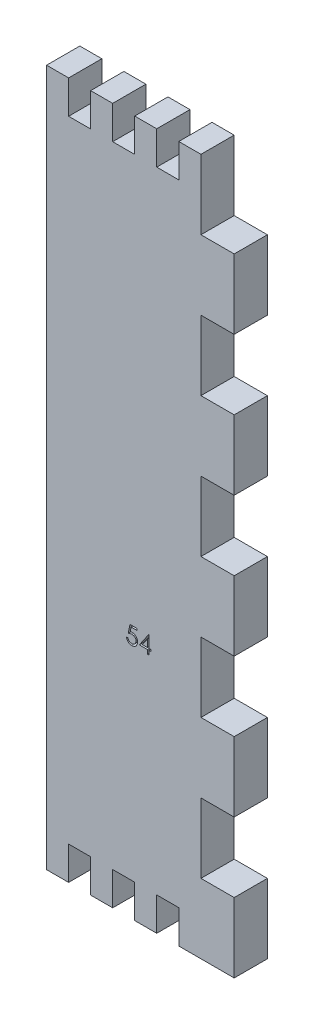
SolidWorks part; units mm, degrees
material "Acrylic (Medium-high impact)"
ref_plane "Front Plane" through (0, 0, 0) normal (0, 0, 1) x (1, 0, 0)
ref_plane "Top Plane" through (0, 0, 0) normal (0, 1, 0) x (1, 0, 0)
ref_plane "Right Plane" through (0, 0, 0) normal (1, 0, 0) x (0, 0, -1)
sketch "Sketch1" plane through (0, 0, 0) normal (0, 0, 1) x (1, 0, 0)
  line L0 (-47.3809, 0) -> (122.7457, 0) construction
  line L1 (0, 130) -> (4.11, 130)
  line L2 (0, 130) -> (0, 0)
  line L3 (0, 0) -> (35, 0)
  line L4 (35, 117) -> (35, 104)
  line L9 (28.8, 52) -> (35, 52)
  line L10 (28.8, 52) -> (28.8, 39)
  line L11 (28.8, 39) -> (35, 39)
  line L17 (28.8, 104) -> (35, 104)
  line L18 (28.8, 104) -> (28.8, 91)
  line L19 (28.8, 91) -> (35, 91)
  line L21 (28.8, 78) -> (35, 78)
  line L22 (28.8, 78) -> (28.8, 65)
  line L23 (28.8, 65) -> (35, 65)
  line L29 (28.8, 26) -> (35, 26)
  line L30 (28.8, 26) -> (28.8, 13)
  line L31 (28.8, 13) -> (35, 13)
  line L34 (28.8, 130) -> (28.8, 117)
  line L35 (28.8, 117) -> (35, 117)
  line L37 (0, 65.7628) -> (0, -41.6741) construction
  line L38 (35, 91) -> (35, 78)
  line L39 (35, 65) -> (35, 52)
  line L40 (35, 39) -> (35, 26)
  line L41 (35, 13) -> (35, 0)
  line L42 (8.22, 130) -> (12.33, 130)
  line L43 (4.11, 0) -> (8.22, 0)
  line L44 (4.11, 0) -> (4.11, 6.2)
  line L45 (4.11, 6.2) -> (8.22, 6.2)
  line L46 (8.22, 0) -> (8.22, 6.2)
  line L47 (12.33, 0) -> (16.44, 0)
  line L48 (12.33, 0) -> (12.33, 6.2)
  line L49 (12.33, 6.2) -> (16.44, 6.2)
  line L50 (16.44, 0) -> (16.44, 6.2)
  line L51 (20.55, 6.2) -> (24.66, 6.2)
  line L52 (20.55, 6.2) -> (20.55, 0)
  line L53 (20.55, 0) -> (24.66, 0)
  line L54 (24.66, 6.2) -> (24.66, 0)
  line L68 (4.11, 130) -> (4.11, 123.8)
  line L69 (4.11, 123.8) -> (8.22, 123.8)
  line L70 (8.22, 130) -> (8.22, 123.8)
  line L72 (12.33, 130) -> (12.33, 123.8)
  line L73 (12.33, 123.8) -> (16.44, 123.8)
  line L74 (16.44, 130) -> (16.44, 123.8)
  line L76 (20.55, 130) -> (20.55, 123.8)
  line L77 (20.55, 123.8) -> (24.66, 123.8)
  line L78 (24.66, 130) -> (24.66, 123.8)
  line L79 (16.44, 130) -> (20.55, 130)
  line L80 (24.66, 130) -> (28.8, 130)
  dimension "D1" = 130
  dimension "D2" = 35
  dimension "D3" = 6.2
  dimension "D4" = 13
  dimension "D5" = 13
  dimension "D6" = 6.2
  dimension "D7" = 13
  dimension "D8" = 6.2
  dimension "D9" = 6.2
  dimension "D10" = 6.2
  dimension "D11" = 13
  dimension "D12" = 13
  dimension "D13" = 13
  dimension "D14" = 13
  dimension "D15" = 13
  dimension "D16" = 13
  dimension "D17" = 6.2
  dimension "D18" = 6.2
  dimension "D19" = 4.11
  dimension "D20" = 4.11
  dimension "D21" = 4.11
  dimension "D22" = 6.2
  dimension "D23" = 4.11
  dimension "D24" = 4.11
  dimension "D25" = 4.11
  dimension "D26" = 6.2
  dimension "D27" = 6.2
  dimension "D28" = 6.2
  dimension "D29" = 4.11
  dimension "D30" = 4.11
  dimension "D31" = 4.11
  dimension "D32" = 4.11
  dimension "D33" = 4.11
  dimension "D34" = 4.11
extrude "Boss-Extrude7" add sketch "Sketch1" along normal blind 6.2 contours L80 L78 L77 L76 L79 L74 L73 L72 L42 L70 L69 L68 L1 L2 L3 L44 L45 L46 L48 L49 L50 L52 L51 L54 L41 L31 L30 L29 L40 L11 L10 L9 L39 L23 L22 L21 L38 L19 L18 L17 L4 L35 L34
sketch "Sketch7" plane through (0, 0, 6.2) normal (0, 0, 1) x (1, 0, 0)
  line L0 (-42.9293, 44.2443) -> (66.2957, 44.2443) construction
  text T0 "         54"
extrude "Cut-Extrude10" cut sketch "Sketch7" against normal blind 1
